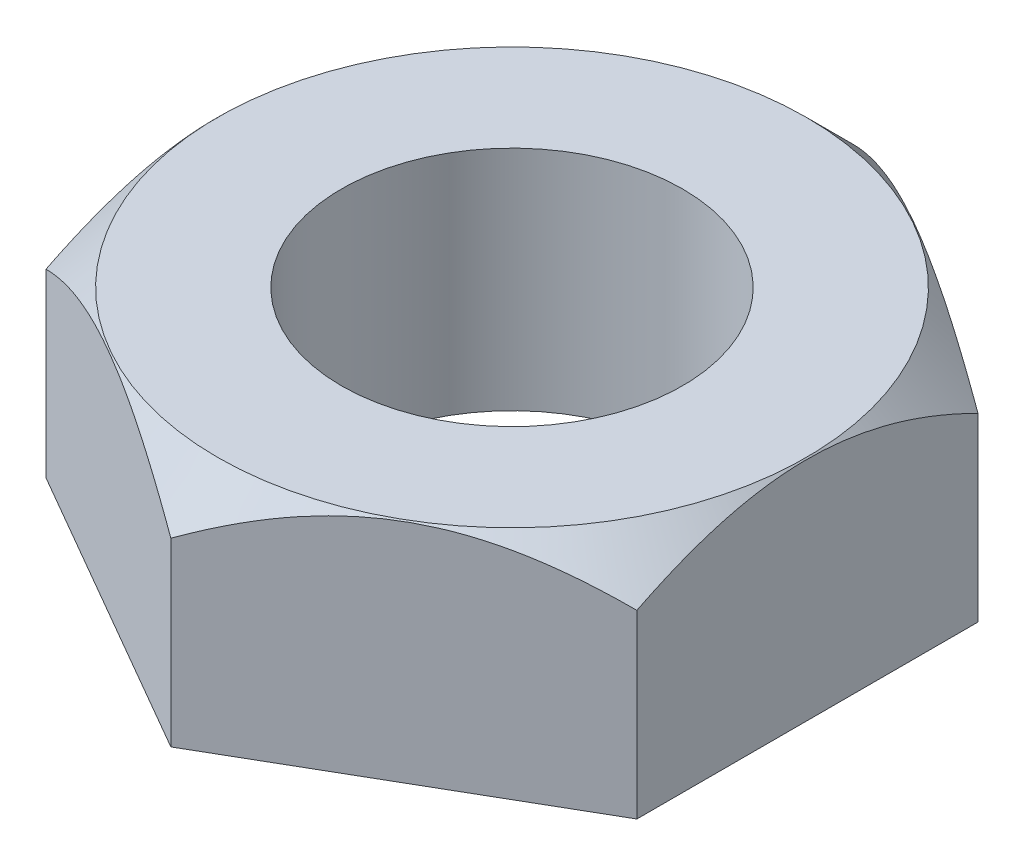
SolidWorks part; units mm, degrees
ref_plane "Front Plane" through (0, 0, 0) normal (0, 0, 1) x (1, 0, 0)
ref_plane "Top Plane" through (0, 0, 0) normal (0, 1, 0) x (1, 0, 0)
ref_plane "Right Plane" through (0, 0, 0) normal (1, 0, 0) x (0, 0, -1)
sketch "Sketch3" plane through (0, 0, 0) normal (0, 1, 0) x (1, 0, 0)
  line L1 (0, -9) -> (7.7942, -4.5)
  line L2 (7.7942, -4.5) -> (7.7942, 4.5)
  line L3 (7.7942, 4.5) -> (0, 9)
  line L4 (0, 9) -> (-7.7942, 4.5)
  line L5 (-7.7942, 4.5) -> (-7.7942, -4.5)
  line L6 (-7.7942, -4.5) -> (0, -9)
  circle A0 centre (0, 0) radius 7.7942 construction
  circle A1 centre (0, 0) radius 4.5
  dimension "D2" = 4.5
  dimension "D1" = 9
extrude "Boss-Extrude2" add sketch "Sketch3" along normal blind 6
sketch "Sketch4" plane through (0, 6, 0) normal (0, 1, 0) x (1, 0, 0)
  circle A0 centre (0, 0) radius 7.7683
  dimension "D1" = 15.5367
extrude "Cut-Extrude1" cut sketch "Sketch4" against normal blind 10 draft 45 flip side to cut
